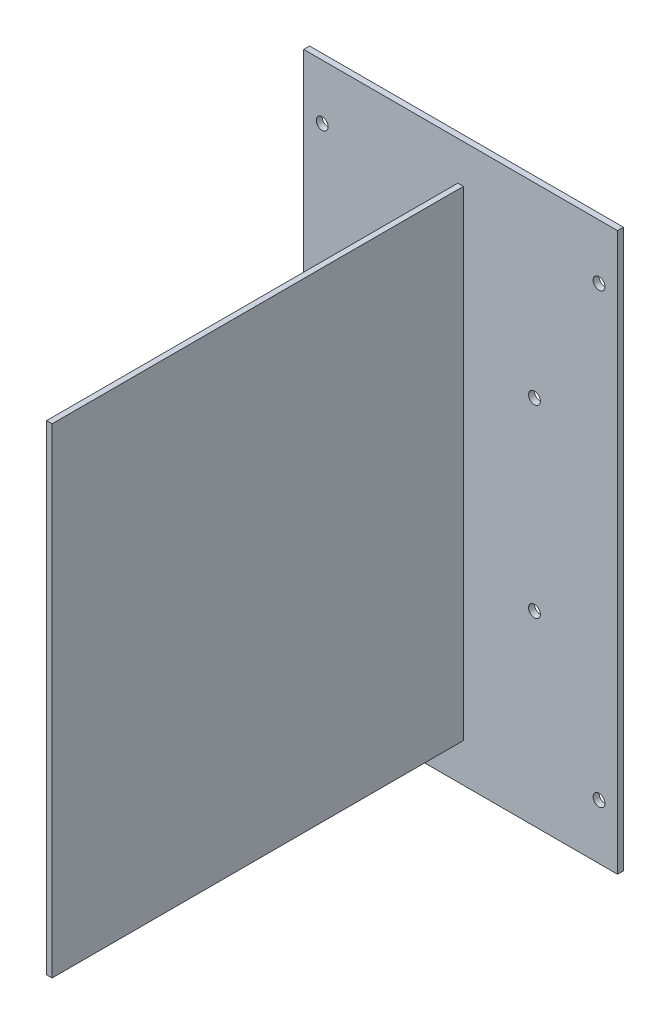
SolidWorks part; units mm, degrees
ref_plane "Front Plane" through (0, 0, 0) normal (0, 0, 1) x (1, 0, 0)
ref_plane "Top Plane" through (0, 0, 0) normal (0, 1, 0) x (1, 0, 0)
ref_plane "Right Plane" through (0, 0, 0) normal (1, 0, 0) x (0, 0, -1)
sketch "Sketch2" plane through (0, 0, 0) normal (0, 0, 1) x (1, 0, 0)
  line L1 (42.5, 75.5) -> (-42.5, 75.5)
  line L2 (42.5, 75.5) -> (42.5, -75.5)
  line L3 (42.5, -75.5) -> (-42.5, -75.5)
  line L4 (-42.5, 75.5) -> (-42.5, -75.5)
  line L5 (42.5, 75.5) -> (-42.5, -75.5) construction
  line L6 (42.5, -75.5) -> (-42.5, 75.5) construction
  line L7 (37.5, -60.6) -> (-37.5, -60.6) construction
  line L8 (37.5, -60.6) -> (37.5, 60.6) construction
  line L9 (37.5, 60.6) -> (-37.5, 60.6) construction
  line L10 (-37.5, -60.6) -> (-37.5, 60.6) construction
  line L11 (37.5, -60.6) -> (-37.5, 60.6) construction
  line L12 (37.5, 60.6) -> (-37.5, -60.6) construction
  line L13 (20, -25) -> (-20, -25) construction
  line L14 (20, -25) -> (20, 25) construction
  line L15 (20, 25) -> (-20, 25) construction
  line L16 (-20, -25) -> (-20, 25) construction
  line L17 (20, -25) -> (-20, 25) construction
  line L18 (20, 25) -> (-20, -25) construction
  circle A0 centre (37.5, 60.6) radius 1.6
  circle A1 centre (-37.5, 60.6) radius 1.6
  circle A2 centre (-37.5, -60.6) radius 1.6
  circle A3 centre (37.5, -60.6) radius 1.6
  circle A4 centre (-20, 25) radius 1.6
  circle A5 centre (20, 25) radius 1.6
  circle A6 centre (20, -25) radius 1.6
  circle A7 centre (-20, -25) radius 1.6
  point P0 (0, 0)
  point P6 (0, 0)
  point P15 (0, 0)
  dimension "D5" = 3.2
  dimension "D6" = 3.2
  dimension "D1" = 85
  dimension "D2" = 151
  dimension "D3" = 75
  dimension "D4" = 121.2
  dimension "D7" = 40
  dimension "D8" = 50
extrude "Boss-Extrude1" add sketch "Sketch2" along normal blind 1.6
sketch "Sketch3" plane through (0, 0, 1.6) normal (0, 0, 1) x (1, 0, 0)
  line L1 (0.75, -65) -> (-0.75, -65)
  line L2 (0.75, -65) -> (0.75, 65)
  line L3 (0.75, 65) -> (-0.75, 65)
  line L4 (-0.75, -65) -> (-0.75, 65)
  line L5 (0.75, -65) -> (-0.75, 65) construction
  line L6 (0.75, 65) -> (-0.75, -65) construction
  point P0 (0, 0)
  dimension "D1" = 130
  dimension "D2" = 1.5
extrude "Cut-Extrude1" cut sketch "Sketch3" against normal blind 1.6
sketch "Sketch4" plane through (0, 0, 0) normal (0, 0, -1) x (-1, 0, 0)
  line L0 (0.75, -65) -> (-0.75, -65) construction
  line L1 (0.75, 65) -> (0.75, -65) construction
  line L2 (-0.75, 65) -> (0.75, 65) construction
  line L3 (-0.75, -65) -> (-0.75, 65) construction
  line L4 (0.75, -65) -> (-0.75, -65)
  line L5 (0.75, 65) -> (0.75, -65)
  line L6 (-0.75, 65) -> (0.75, 65)
  line L7 (-0.75, -65) -> (-0.75, 65)
extrude "Boss-Extrude2" add sketch "Sketch4" against normal blind 113 separate body
